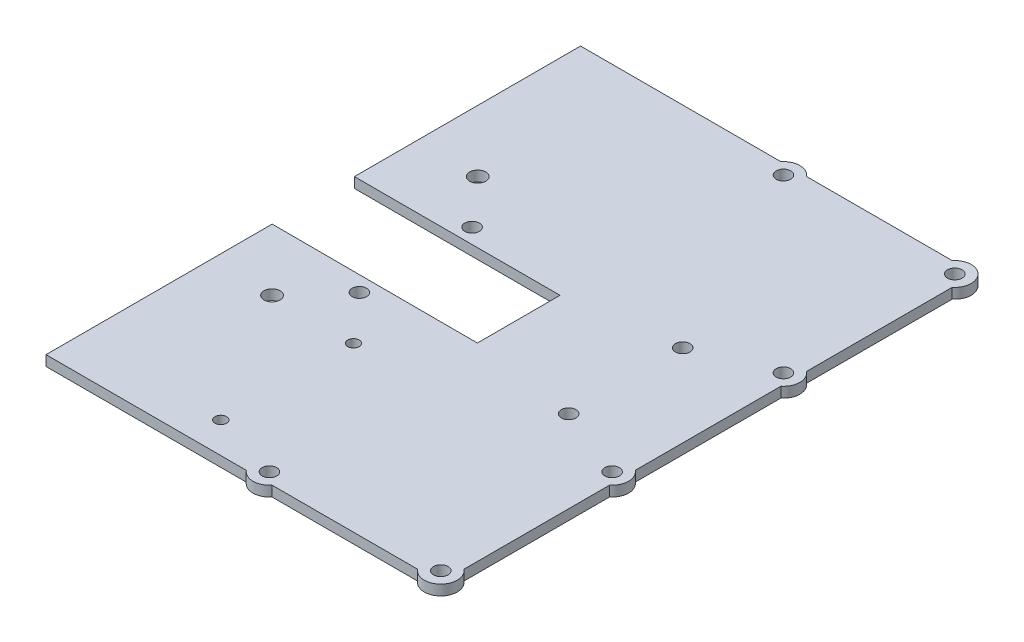
SolidWorks part; units mm, degrees
material "Aluminum"
ref_plane "Front Plane" through (0, 0, 0) normal (0, 0, 1) x (1, 0, 0)
ref_plane "Top Plane" through (0, 0, 0) normal (0, 1, 0) x (1, 0, 0)
ref_plane "Right Plane" through (0, 0, 0) normal (1, 0, 0) x (0, 0, -1)
sketch "Sketch1" plane through (0, 0, 0) normal (0, 1, 0) x (1, 0, 0)
  circle A0 centre (65.8401, 3.175) radius 2.2479
  circle A1 centre (118.7568, 3.175) radius 2.2479
  circle A2 centre (118.7568, 56.0917) radius 2.2479
  circle A3 centre (118.7568, 109.0083) radius 2.2479
  circle A4 centre (118.7568, 161.925) radius 2.2479
  circle A5 centre (65.8401, 161.925) radius 2.2479
  line B0 (0, 165.1) -> (61.8745, 165.1)
  line B1 (0, 95.25) -> (0, 165.1)
  line B2 (0, 69.85) -> (0, 0)
  line B3 (61.8745, 0) -> (0, 0)
  line B4 (114.7912, 0) -> (69.8057, 0)
  line B5 (121.9318, 52.1261) -> (121.9318, 7.1406)
  line B6 (121.9318, 105.0428) -> (121.9318, 60.0572)
  line B7 (121.9318, 157.9594) -> (121.9318, 112.9739)
  line B8 (69.8057, 165.1) -> (114.7912, 165.1)
  line B9 (0, 95.25) -> (63.5, 95.25)
  line B10 (63.5, 95.25) -> (63.5, 69.7245)
  line B11 (63.5, 69.7245) -> (0, 69.85)
  arc B12 (69.8057, 165.1) -> (61.8745, 165.1) centre (65.8401, 161.925) ccw
  arc B13 (61.8745, 0) -> (69.8057, 0) centre (65.8401, 3.175) ccw
  arc B14 (114.7912, 0) -> (121.9318, 7.1406) centre (118.7568, 3.175) ccw
  arc B15 (121.9318, 52.1261) -> (121.9318, 60.0572) centre (118.7568, 56.0917) ccw
  arc B16 (121.9318, 105.0428) -> (121.9318, 112.9739) centre (118.7568, 109.0083) ccw
  arc B17 (121.9318, 157.9594) -> (114.7912, 165.1) centre (118.7568, 161.925) ccw
  dimension "D1" = 4.4958
sketch_block_instance "Block-bottomplate-1"
sketch_block "Block-bottomplate" parameters "D1"=63.5, "D2"=69.85
extrude "Boss-Extrude1" add sketch "Sketch1" along normal blind 3.175
sketch "Sketch2" plane through (0, 0, 0) normal (0, -1, 0) x (1, 0, 0)
  line L0 (63.5, -69.7245) -> (0, -69.85) construction
  line L1 (0, -95.25) -> (63.5, -95.25) construction
  line L2 (0, -165.1) -> (0, -95.25) construction
  line L3 (0, -65.0875) -> (121.9318, -64.8465) construction
  line L4 (0, -69.85) -> (0, 0) construction
  line L5 (121.9318, -60.0572) -> (121.9318, -105.0428) construction
  line L6 (121.9318, -82.55) -> (63.5, -82.4872) construction
  line L7 (63.5, -95.25) -> (63.5, -69.7245) construction
  circle A0 centre (19.05, -50.7623) radius 2.4892
  circle A1 centre (19.05, -114.3) radius 2.4892
  circle A2 centre (31.75, -65.0247) radius 2.2479
  circle A3 centre (96.5318, -64.8967) radius 2.2479
  circle A4 centre (96.4939, -100.1487) radius 2.2479
  circle A5 centre (31.7126, -99.8815) radius 2.2479
  dimension "D3" = 4.9784
  dimension "D5" = 4.4958
  dimension "D6" = 4.4958
  dimension "D1" = 19.05
  dimension "D2" = 19.05
  dimension "D4" = 19.05
  dimension "D7" = 4.7625
  dimension "D8" = 31.75
  dimension "D9" = 25.4
extrude "Cut-Extrude1" cut sketch "Sketch2" against normal through all
sketch "Sketch3" plane through (0, 3.175, 0) normal (0, 1, 0) x (1, 0, 0)
  line L1 (0, 69.85) -> (0, 0) construction
  line L2 (0, 0) -> (61.8745, 0) construction
  circle A0 centre (44.45, 9.525) radius 1.778
  circle A1 centre (44.45, 50.525) radius 1.778
  point P8 (0, 0)
  dimension "D1" = 3.556
  dimension "D2" = 3.556
  dimension "D3" = 41
  dimension "D4" = 9.525
  dimension "D5" = 44.45
extrude "Cut-Extrude2" cut sketch "Sketch3" against normal through all
equation "\"Unit Measure\"= \"BoundingVolume\" / \"Thickness\"'in^2"
